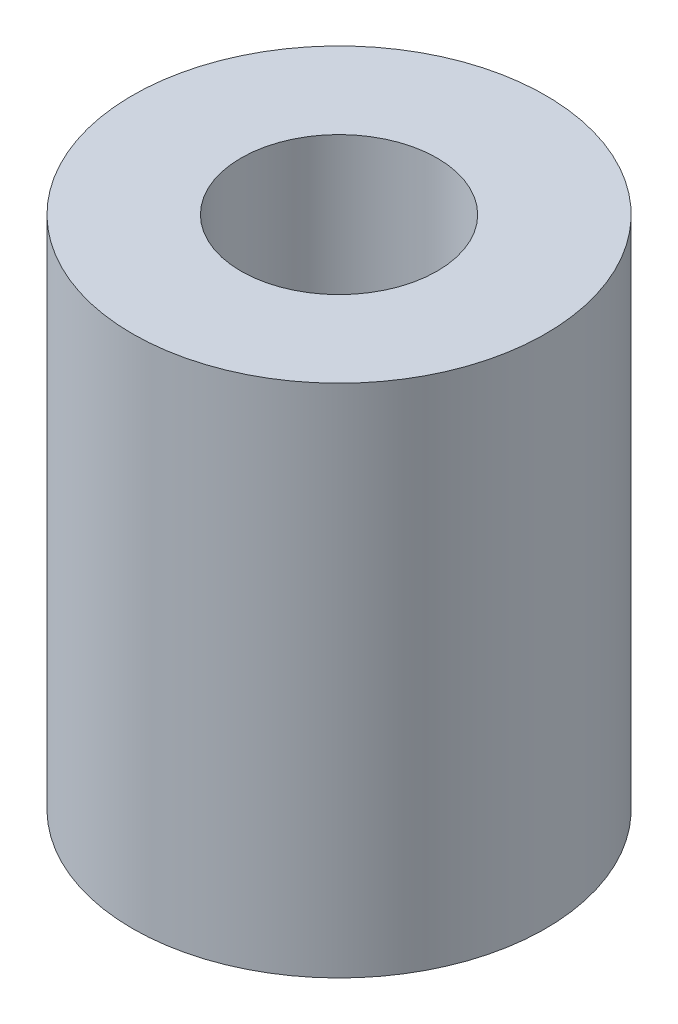
SolidWorks part; units mm, degrees
material "6061-T6 (SS)"
ref_plane "Front Plane" through (0, 0, 0) normal (0, 0, 1) x (1, 0, 0)
ref_plane "Top Plane"
ref_plane "Right Plane" through (0, 0, 0) normal (1, 0, 0) x (0, 0, -1)
sketch "Sketch1" plane through (0, 0, 0) normal (0, 1, 0) x (1, 0, 0)
  circle A0 centre (0, 0) radius 10.033
  dimension "D1" = 20.066
extrude "Boss-Extrude1" add sketch "Sketch1" along normal blind 25.019
sketch "Sketch2" plane through (0, 0, 0) normal (0, -1, 0) x (1, 0, 0)
  circle A0 centre (0, 0) radius 4
  dimension "D1" = 8
extrude "Cut-Extrude1" cut sketch "Sketch2" against normal blind 10.16
sketch "Sketch3" plane through (0, 25.019, 0) normal (0, 1, 0) x (1, 0, 0)
  circle A0 centre (0, 0) radius 4.7625
  dimension "D1" = 9.525
extrude "Cut-Extrude2" cut sketch "Sketch3" against normal up to surface (14.859 mm away) up to face at (0, 10.16, -4)
